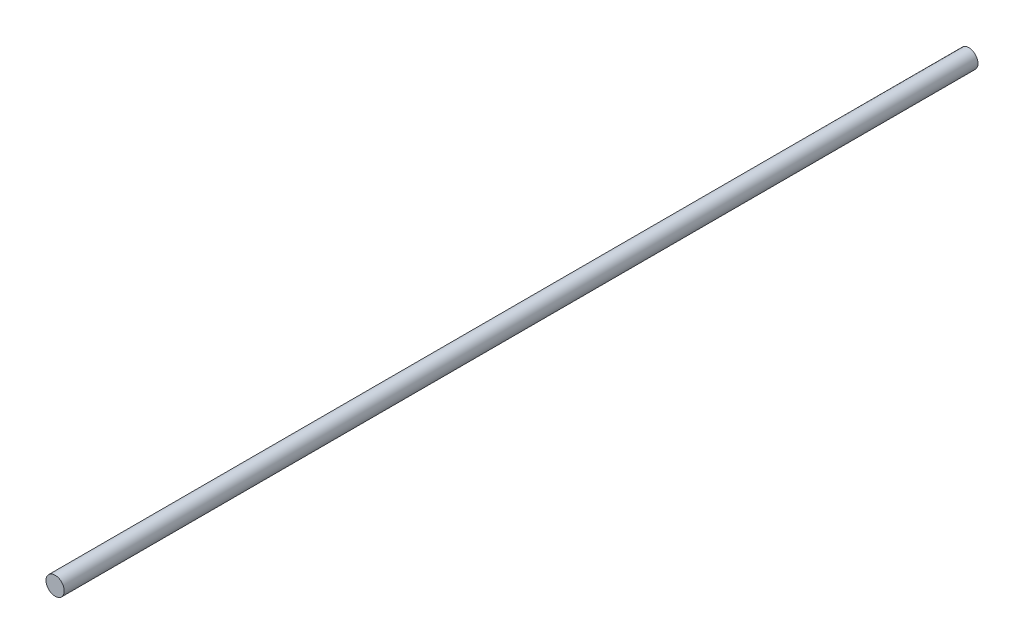
SolidWorks part; units mm, degrees
material "Plain Carbon Steel"
ref_plane "Front Plane" through (0, 0, 0) normal (0, 0, 1) x (1, 0, 0)
ref_plane "Top Plane" through (0, 0, 0) normal (0, 1, 0) x (1, 0, 0)
ref_plane "Right Plane" through (0, 0, 0) normal (1, 0, 0) x (0, 0, -1)
sketch "Sketch1" plane through (0, 0, 0) normal (0, 0, 1) x (1, 0, 0)
  circle A0 centre (0, 0) radius 2.5
  dimension "D1" = 5
extrude "Boss-Extrude1" add sketch "Sketch1" along normal blind 250
